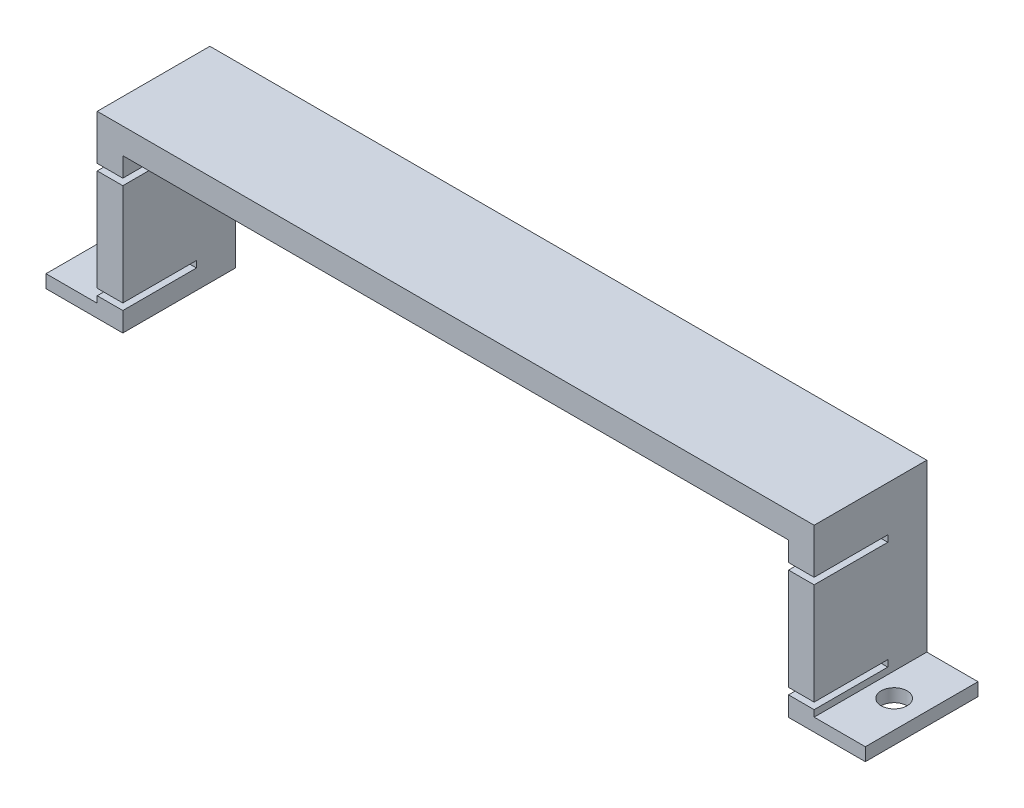
SolidWorks part; units mm, degrees
ref_plane "Front Plane" through (0, 0, 0) normal (0, 0, 1) x (1, 0, 0)
ref_plane "Top Plane" through (0, 0, 0) normal (0, 1, 0) x (1, 0, 0)
ref_plane "Right Plane" through (0, 0, 0) normal (1, 0, 0) x (0, 0, -1)
sketch "Sketch1" plane through (0, 0, 0) normal (0, 1, 0) x (1, 0, 0)
  line L1 (0, 0) -> (160, 0)
  line L2 (0, 0) -> (0, 22)
  line L3 (0, 22) -> (160, 22)
  line L4 (160, 0) -> (160, 22)
  dimension "D1" = 22
  dimension "D2" = 160
extrude "Boss-Extrude1" add sketch "Sketch1" along normal blind 35
sketch "Sketch4" plane through (0, 0, 0) normal (0, 0, 1) x (1, 0, 0)
  line L0 (0, 0) -> (160, 0) construction
  line L1 (15, 0) -> (145, 0)
  line L2 (15, 0) -> (15, 30)
  line L3 (15, 30) -> (145, 30)
  line L4 (145, 0) -> (145, 30)
  line L5 (80, 35) -> (80, 0) construction
  line L6 (0, 35) -> (160, 35) construction
  dimension "D1" = 130
  dimension "D2" = 5
extrude "Cut-Extrude3" cut sketch "Sketch4" against normal through all
sketch "Sketch5" plane through (0, 0, 0) normal (0, 0, 1) x (1, 0, 0)
  line L0 (80, 35) -> (80, 0) construction
  line L1 (0, 35) -> (10, 35)
  line L2 (0, 35) -> (0, 2.54)
  line L3 (0, 2.54) -> (10, 2.54)
  line L4 (10, 35) -> (10, 2.54)
  line L5 (0, 35) -> (160, 35) construction
  line L6 (15, 30) -> (15, 0) construction
  line L7 (0, 0) -> (15, 0) construction
  line L8 (150, 35) -> (150, 2.54)
  line L9 (160, 2.54) -> (150, 2.54)
  line L10 (160, 35) -> (160, 2.54)
  line L11 (160, 35) -> (150, 35)
  dimension "D1" = 5
  dimension "D2" = 2.54
extrude "Cut-Extrude4" cut sketch "Sketch5" against normal through all
sketch "Sketch7" plane through (10, 0, 0) normal (-1, 0, 0) x (0, 0, 1)
  line L0 (0, 2.54) -> (0, 35) construction
  line L1 (0, 3.81) -> (-14.38, 3.81)
  line L2 (0, 3.81) -> (0, 5.08)
  line L3 (0, 5.08) -> (-14.38, 5.08)
  line L4 (-14.38, 3.81) -> (-14.38, 5.08)
  line L5 (-22, 0) -> (0, 0) construction
  line L6 (-22, 2.54) -> (-22, 35) construction
  line L7 (0, 15) -> (-22, 15) construction
  line L9 (-14.38, 26.19) -> (-14.38, 24.92)
  line L10 (0, 24.92) -> (-14.38, 24.92)
  line L11 (0, 26.19) -> (0, 24.92)
  line L12 (0, 26.19) -> (-14.38, 26.19)
  line L13 (-22, 30) -> (0, 30) construction
  dimension "D1" = 3.81
  dimension "D2" = 7.62
  dimension "D3" = 1.27
  dimension "D4" = 3.81
extrude "Cut-Extrude5" cut sketch "Sketch7" against normal through all
sketch "Sketch8" plane through (0, 2.54, 0) normal (0, 1, 0) x (1, 0, 0)
  line L0 (160, 11) -> (0, 11) construction
  line L1 (160, 22) -> (160, 0) construction
  line L2 (0, 22) -> (0, 0) construction
  line L4 (5, 22) -> (5, 0) construction
  line L5 (0, 22) -> (10, 22) construction
  line L6 (0, 0) -> (10, 0) construction
  circle A0 centre (154.6214, 11) radius 2.54
  circle A1 centre (5, 11) radius 2.54
  dimension "D1" = 5.08
extrude "Cut-Extrude6" cut sketch "Sketch8" against normal through all
